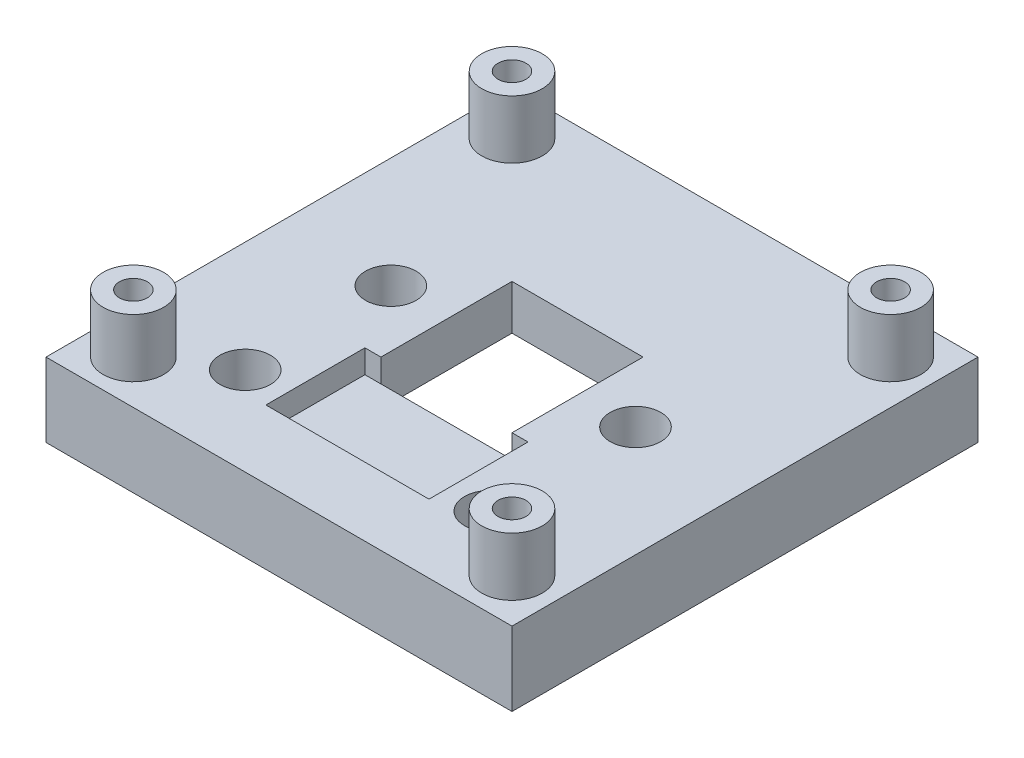
SolidWorks part; units mm, degrees
ref_plane "Front Plane" through (0, 0, 0) normal (0, 0, 1) x (1, 0, 0)
ref_plane "Top Plane" through (0, 0, 0) normal (0, 1, 0) x (1, 0, 0)
ref_plane "Right Plane" through (0, 0, 0) normal (1, 0, 0) x (0, 0, -1)
sketch "Sketch1" plane through (0, 0, 0) normal (0, 1, 0) x (1, 0, 0)
  line L1 (-20, 20) -> (20, 20)
  line L2 (-20, 20) -> (-20, -20)
  line L3 (-20, -20) -> (20, -20)
  line L4 (20, 20) -> (20, -20)
  line L5 (-20, 20) -> (20, -20) construction
  line L6 (-20, -20) -> (20, 20) construction
  point P0 (0, 0)
  dimension "D1" = 40
  dimension "D2" = 40
extrude "Boss-Extrude1" add sketch "Sketch1" along normal blind 6.35
sketch "Sketch2" plane through (0, 6.35, 0) normal (0, 1, 0) x (1, 0, 0)
  line L1 (-5.625, -5.625) -> (5.625, -5.625)
  line L2 (-5.625, -5.625) -> (-5.625, 5.625)
  line L3 (-5.625, 5.625) -> (5.625, 5.625)
  line L4 (5.625, -5.625) -> (5.625, 5.625)
  line L5 (-5.625, -5.625) -> (5.625, 5.625) construction
  line L6 (-5.625, 5.625) -> (5.625, -5.625) construction
  point P0 (0, 0)
  dimension "D1" = 11.25
extrude "Cut-Extrude1" cut sketch "Sketch2" against normal through all
sketch "Sketch3" plane through (0, 6.35, 0) normal (0, 1, 0) x (1, 0, 0)
  line L0 (0, 0) -> (0, 2.7158) construction
  line L1 (-7, -5.625) -> (7, -5.625)
  line L2 (-7, -5.625) -> (-7, -14.125)
  line L3 (-7, -14.125) -> (7, -14.125)
  line L4 (7, -5.625) -> (7, -14.125)
  line L6 (-5.625, -5.625) -> (5.625, -5.625) construction
  point P5 (0, -5.625)
  dimension "D1" = 14
  dimension "D2" = 8.5
extrude "Cut-Extrude2" cut sketch "Sketch3" against normal blind 2
sketch "Sketch4" plane through (0, 6.35, 0) normal (0, 1, 0) x (1, 0, 0)
  line L0 (0, 0) -> (0, 9.1234) construction
  line L2 (-12.5, 9.462) -> (12.5, 9.462) construction
  line L3 (-12.5, 9.462) -> (-12.5, -14.4) construction
  line L4 (-12.5, -14.4) -> (12.5, -14.4) construction
  line L5 (12.5, 9.462) -> (12.5, -14.4) construction
  point P7 (0, 9.462)
  point P8 (10.5, -12.4)
  point P9 (-10.5, -12.4)
  point P10 (-10.5, 0.1)
  point P11 (10.5, 0.1)
  dimension "D1" = 14.4
  dimension "D2" = 23.862
  dimension "D3" = 25
  dimension "D4" = 2
  dimension "D5" = 2
  dimension "D6" = 14.5
hole_wizard "M2 Clearance Hole1" positions "Sketch4" profile "Sketch5" hole size "M2" standard "ANSI Metric" end condition through all
sketch "Sketch5" plane through (10.5, 6.35, -0.1) normal (1, 0, 0) x (0, 0, 1)
  line L0 (0, 0) -> (0, 6.35)
  line L1 (0, 6.35) -> (1.2, 6.35)
  line L2 (1.2, 6.35) -> (1.2, 0)
  line L5 (1.2, 0) -> (0, 0)
  line L11 (0, -6.35) -> (0, 107.95) construction
  dimension "Thru Hole Dia." = 2.4
  dimension "Thru Hole Depth" = 6.35
sketch "Sketch6" plane through (0, 6.35, 0) normal (0, 1, 0) x (1, 0, 0)
  line L1 (-16.25, -16.25) -> (16.25, -16.25) construction
  line L2 (-16.25, -16.25) -> (-16.25, 16.25) construction
  line L3 (-16.25, 16.25) -> (16.25, 16.25) construction
  line L4 (16.25, -16.25) -> (16.25, 16.25) construction
  line L5 (-16.25, -16.25) -> (16.25, 16.25) construction
  line L6 (-16.25, 16.25) -> (16.25, -16.25) construction
  circle A0 centre (-16.25, 16.25) radius 2.6
  circle A1 centre (16.25, 16.25) radius 2.6
  circle A2 centre (16.25, -16.25) radius 2.6
  circle A3 centre (-16.25, -16.25) radius 2.6
  point P0 (0, 0)
  dimension "D2" = 5.2
  dimension "D1" = 32.5
extrude "Boss-Extrude2" add sketch "Sketch6" along normal blind 5
sketch "Sketch10" plane through (0, 0, 0) normal (0, -1, 0) x (1, 0, 0)
  circle A0 centre (16.25, 16.25) radius 2.6 construction
  circle A1 centre (16.25, -16.25) radius 2.6 construction
  circle A2 centre (-16.25, -16.25) radius 2.6 construction
  circle A3 centre (-16.25, 16.25) radius 2.6 construction
  circle A4 centre (16.25, 16.25) radius 2.6 construction
  circle A5 centre (16.25, -16.25) radius 2.6 construction
  circle A6 centre (-16.25, -16.25) radius 2.6 construction
  circle A7 centre (-16.25, 16.25) radius 2.6 construction
  point P13 (-16.25, 16.25)
  point P14 (16.25, 16.25)
  point P15 (16.25, -16.25)
  point P16 (-16.25, -16.25)
hole_wizard "CBORE for M2 SHCS1" positions "Sketch10" profile "Sketch11" counterbore size "M2" standard "ANSI Metric" end condition through all
sketch "Sketch11" plane through (-16.25, 0, -16.25) normal (1, 0, 0) x (0, 0, -1)
  line L0 (0, 0) -> (0, 11.35)
  line L1 (0, 11.35) -> (1.2, 11.35)
  line L3 (1.2, 11.35) -> (1.2, 2)
  line L4 (1.2, 2) -> (2.2, 2)
  line L5 (2.2, 2) -> (2.2, 0)
  line L7 (2.2, 0) -> (0, 0)
  line L11 (0, -6.35) -> (0, 107.95) construction
  dimension "Thru Hole Dia." = 2.4
  dimension "Thru Hole Depth" = 11.35
  dimension "C'Bore Dia." = 4.4
  dimension "C'Bore Depth" = 2
sketch "Sketch12" plane through (0, 0, 0) normal (0, 0, 1) x (1, 0, 0)
  line L0 (20, 6.35) -> (20, 0) construction
  line L1 (-20, 6.35) -> (20, 6.35)
  line L2 (-20, 6.35) -> (-20, 11.35)
  line L3 (-20, 11.35) -> (20, 11.35)
  line L4 (20, 6.35) -> (20, 11.35)
  line L5 (-13.65, 11.35) -> (-18.85, 11.35) construction
extrude "Cut-Extrude3" [suppressed] cut sketch "Sketch12" against normal through all and the other way through all
sketch "Sketch13" plane through (0, 6.35, 0) normal (0, 1, 0) x (1, 0, 0)
  line L0 (0, 0) -> (0, -5.9289) construction
  circle A0 centre (-10.5, -12.4) radius 2.175
  circle A1 centre (-10.5, 0.1) radius 2.175
  circle A2 centre (10.5, -12.4) radius 2.175
  circle A3 centre (10.5, 0.1) radius 2.175
  dimension "D1" = 4.35
extrude "Cut-Extrude4" cut sketch "Sketch13" against normal blind 4.2
chamfer "Chamfer1" distance 2.5 angle 45 4 edges at (0, 0, -5.625) (5.625, 0, 0) (-5.625, 0, 0) (0, 0, 5.625)
